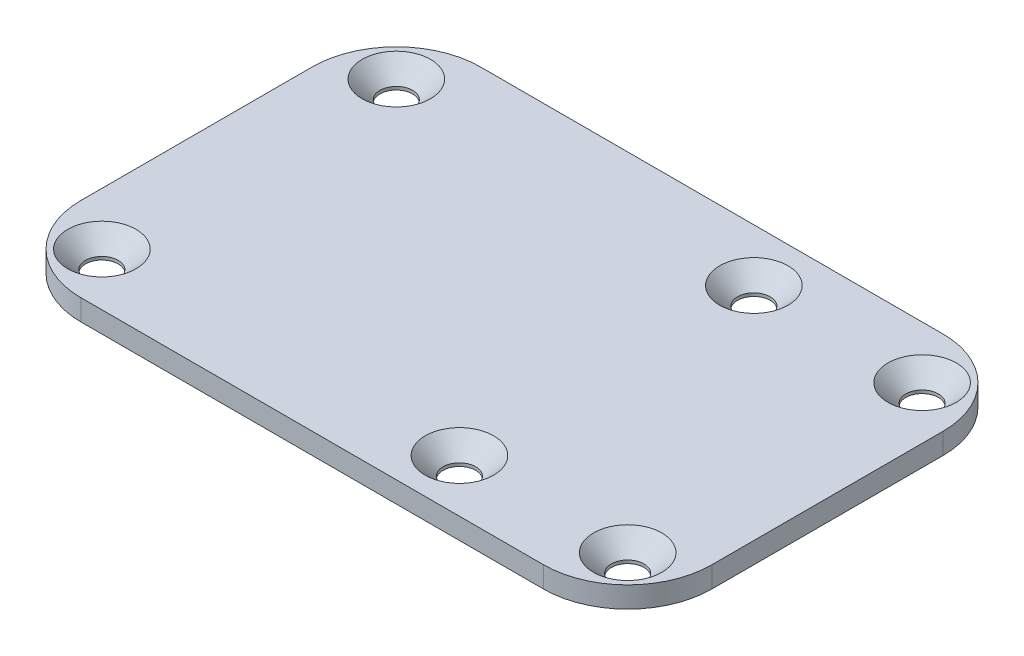
SolidWorks part; units mm, degrees
material "6063-T6"
ref_plane "Front Plane" through (0, 0, 0) normal (0, 0, 1) x (1, 0, 0)
ref_plane "Top Plane" through (0, 0, 0) normal (0, 1, 0) x (1, 0, 0)
ref_plane "Right Plane" through (0, 0, 0) normal (1, 0, 0) x (0, 0, -1)
sketch "Sketch1" plane through (0, 0, 0) normal (0, 1, 0) x (1, 0, 0)
  line L1 (22, -19) -> (-22, -19)
  line L2 (30, -11) -> (30, 11)
  line L3 (22, 19) -> (-22, 19)
  line L4 (-30, -11) -> (-30, 11)
  line L5 (30, -19) -> (-30, 19) construction
  line L6 (30, 19) -> (-30, -19) construction
  arc A0 (30, 11) -> (22, 19) centre (22, 11) ccw
  arc A1 (22, -19) -> (30, -11) centre (22, -11) ccw
  arc A2 (-22, -19) -> (-30, -11) centre (-22, -11) cw
  arc A3 (-22, 19) -> (-30, 11) centre (-22, 11) ccw
  point P0 (0, 0)
  dimension "D3" = 8
  dimension "D1" = 60
  dimension "D2" = 38
extrude "Boss-Extrude1" add sketch "Sketch1" along normal blind 2
hole_wizard "Ø3.1 (3.1) Diameter Hole1" positions "Location" profile "Hole" hole size "Ø3.1" standard "ANSI Metric" end condition through all
sketch "Location" plane through (0, 2, 0) normal (0, -1, 0) x (-1, 0, 0)
  line L4 (-33.1926, 0) -> (33.4931, 0) construction
  line L6 (0, 17.9223) -> (0, -17.6691) construction
  point P0 (-25, 14)
  point P2 (-25, -14)
  point P4 (25, -14)
  point P6 (25, 14)
  point P29 (-9, 14)
  point P31 (-9, -14)
  dimension "D1" = 28
  dimension "D2" = 25
  dimension "D3" = 25
  dimension "D4" = 16
sketch "Hole" plane through (25, 2, -14) normal (1, 0, 0) x (0, 0, 1)
  line L0 (0, 0) -> (0, 2)
  line L1 (0, 2) -> (1.55, 2)
  line L2 (1.55, 2) -> (1.55, 1.7)
  line L3 (1.55, 1.7) -> (3.25, 0)
  line L5 (3.25, 0) -> (0, 0)
  line L6 (-1.55, 1.7) -> (-3.25, 0) construction
  line L11 (0, -6.35) -> (0, 107.95) construction
  dimension "Thru Hole Dia." = 3.1
  dimension "Thru Hole Depth" = 2
  dimension "Near C'Sink Dia." = 6.5
  dimension "Near C'Sink Angle" = 90
